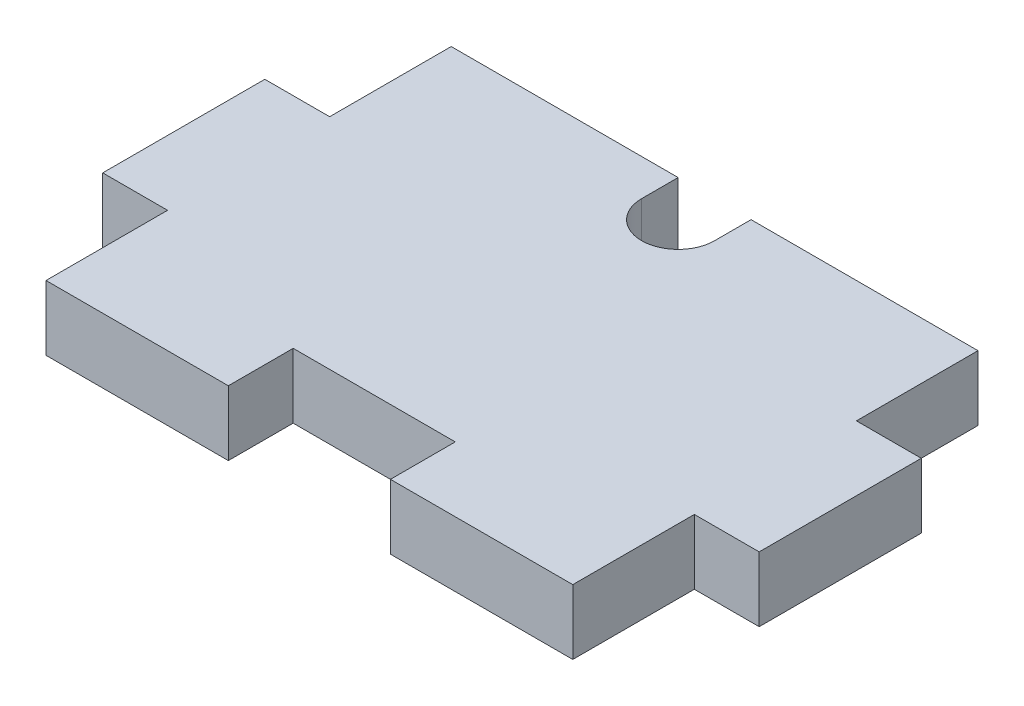
SolidWorks part; units mm, degrees
material "Maple"
ref_plane "Front Plane" through (0, 0, 0) normal (0, 0, 1) x (1, 0, 0)
ref_plane "Top Plane" through (0, 0, 0) normal (0, 1, 0) x (1, 0, 0)
ref_plane "Right Plane" through (0, 0, 0) normal (1, 0, 0) x (0, 0, -1)
sketch "Sketch1" plane through (0, 0, 0) normal (0, 1, 0) x (1, 0, 0)
  line L1 (0, 0) -> (32.5, 0)
  line L2 (0, 0) -> (0, -25)
  line L3 (0, -25) -> (32.5, -25)
  line L4 (32.5, 0) -> (32.5, -25)
  dimension "D1" = 32.5
  dimension "D2" = 25
extrude "Boss-Extrude1" add sketch "Sketch1" along normal blind 4
sketch "Sketch2" plane through (0, 4, 0) normal (0, 1, 0) x (1, 0, 0)
  line L0 (16.25, 0) -> (16.25, -25) construction
  line L1 (32.5, 0) -> (0, 0) construction
  line L2 (0, -25) -> (32.5, -25) construction
  line L4 (14, -2.25) -> (18.5, -2.25)
  line L5 (14, -2.25) -> (14, 0)
  line L6 (14, 0) -> (18.5, 0)
  line L7 (18.5, -2.25) -> (18.5, 0)
  circle A0 centre (16.25, -2.25) radius 2.25
  line M4 (32.5, 0) -> (0, 0)
  dimension "D1" = 4.5
extrude "Cut-Extrude5" cut sketch "Sketch2" against normal through all contours L0 L4 A0 | L0 A0 L4 | A0 L6 L5 | A0 L7 M4 | A0 L0 L4 | L4 L0 A0
sketch "Sketch3" plane through (0, 4, 0) normal (0, 1, 0) x (1, 0, 0)
  line L0 (0, -12.5) -> (32.5, -12.5) construction
  line L1 (0, 0) -> (0, -25) construction
  line L2 (32.5, -25) -> (32.5, 0) construction
  line L4 (-4, -7.5) -> (0, -7.5)
  line L5 (-4, -7.5) -> (-4, -17.5)
  line L6 (-4, -17.5) -> (0, -17.5)
  line L7 (0, -7.5) -> (0, -17.5)
  line L8 (-4, -7.5) -> (0, -17.5) construction
  line L9 (-4, -17.5) -> (0, -7.5) construction
  line L10 (32.5, -7.5) -> (36.5, -7.5)
  line L11 (32.5, -7.5) -> (32.5, -17.5)
  line L12 (32.5, -17.5) -> (36.5, -17.5)
  line L13 (36.5, -7.5) -> (36.5, -17.5)
  line L14 (32.5, -7.5) -> (36.5, -17.5) construction
  line L15 (32.5, -17.5) -> (36.5, -7.5) construction
  point P6 (-2, -12.5)
  point P11 (34.5, -12.5)
  dimension "D1" = 4
  dimension "D2" = 10
  dimension "D3" = 10
  dimension "D4" = 4
extrude "Boss-Extrude2" add sketch "Sketch3" against normal through all
sketch "Sketch4" plane through (0, 4, 0) normal (0, 1, 0) x (1, 0, 0)
  line L0 (0, -25) -> (32.5, -25) construction
  line L1 (11.25, -21) -> (21.25, -21)
  line L2 (11.25, -21) -> (11.25, -25)
  line L3 (11.25, -25) -> (21.25, -25)
  line L4 (21.25, -21) -> (21.25, -25)
extrude "Cut-Extrude6" cut sketch "Sketch4" against normal through all
equation "\"D3@Sketch3\"=\"D2@Sketch3\""
equation "\"D4@Sketch3\"=\"D1@Sketch3\""
